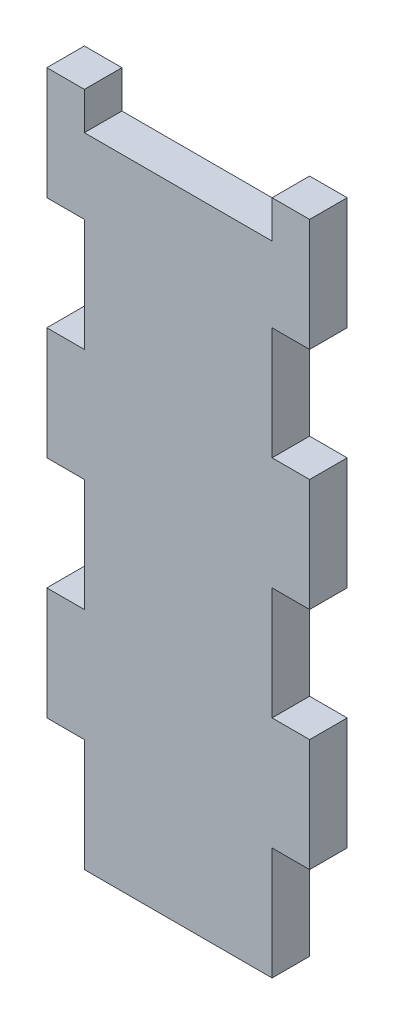
SolidWorks part; units mm, degrees
ref_plane "Front Plane" through (0, 0, 0) normal (0, 0, 1) x (1, 0, 0)
ref_plane "Top Plane" through (0, 0, 0) normal (0, 1, 0) x (1, 0, 0)
ref_plane "Right Plane" through (0, 0, 0) normal (1, 0, 0) x (0, 0, -1)
sketch "Model" plane through (0, 0, 0) normal (0, 0, 1) x (1, 0, 0)
  line L0 (54.8215, 115.3245) -> (60.8215, 115.3245)
  line L1 (60.8215, 115.3245) -> (60.8215, 97.3245)
  line L2 (60.8215, 97.3245) -> (54.8215, 97.3245)
  line L3 (54.8215, 97.3245) -> (54.8215, 79.3245)
  line L4 (60.8215, 79.3245) -> (60.8215, 61.3245)
  line L5 (60.8215, 61.3245) -> (54.8215, 61.3245)
  line L6 (54.8215, 61.3245) -> (54.8215, 43.3245)
  line L7 (60.8215, 43.3245) -> (60.8215, 25.3245)
  line L8 (60.8215, 25.3245) -> (54.8215, 25.3245)
  line L9 (54.8215, 25.3245) -> (54.8215, 7.3245)
  line L10 (60.8215, 79.3245) -> (54.8215, 79.3245)
  line L11 (54.8215, 43.3245) -> (60.8215, 43.3245)
  line L12 (18.8215, 115.3245) -> (18.8215, 97.3245)
  line L13 (18.8215, 97.3245) -> (24.8215, 97.3245)
  line L14 (24.8215, 97.3245) -> (24.8215, 79.3245)
  line L15 (18.8215, 79.3245) -> (18.8215, 61.3245)
  line L16 (18.8215, 61.3245) -> (24.8215, 61.3245)
  line L17 (24.8215, 61.3245) -> (24.8215, 43.3245)
  line L18 (18.8215, 43.3245) -> (18.8215, 25.3245)
  line L19 (18.8215, 25.3245) -> (24.8215, 25.3245)
  line L20 (18.8215, 79.3245) -> (24.8215, 79.3245)
  line L21 (24.8215, 43.3245) -> (18.8215, 43.3245)
  line L22 (24.8215, 15.3245) -> (24.8215, 25.3245)
  line L23 (18.8215, 115.3245) -> (24.8215, 115.3245)
  line L24 (24.8215, 115.3245) -> (24.8215, 109.3245)
  line L25 (24.8215, 109.3245) -> (54.8215, 109.3245)
  line L26 (54.8215, 109.3245) -> (54.8215, 115.3245)
  line L27 (24.8215, 15.3245) -> (24.8215, 7.3245)
  line L28 (54.8215, 7.3245) -> (24.8215, 7.3245)
extrude "Boss-Extrude1" add sketch "Model" along normal blind 6 contours L15 L16 L17 L21 L18 L19 L22 L27 L28 L9 L8 L7 L11 L6 L5 L4 L10 L3 L2 L1 L0 L26 L25 L24 L23 L12 L13 L14 L20
